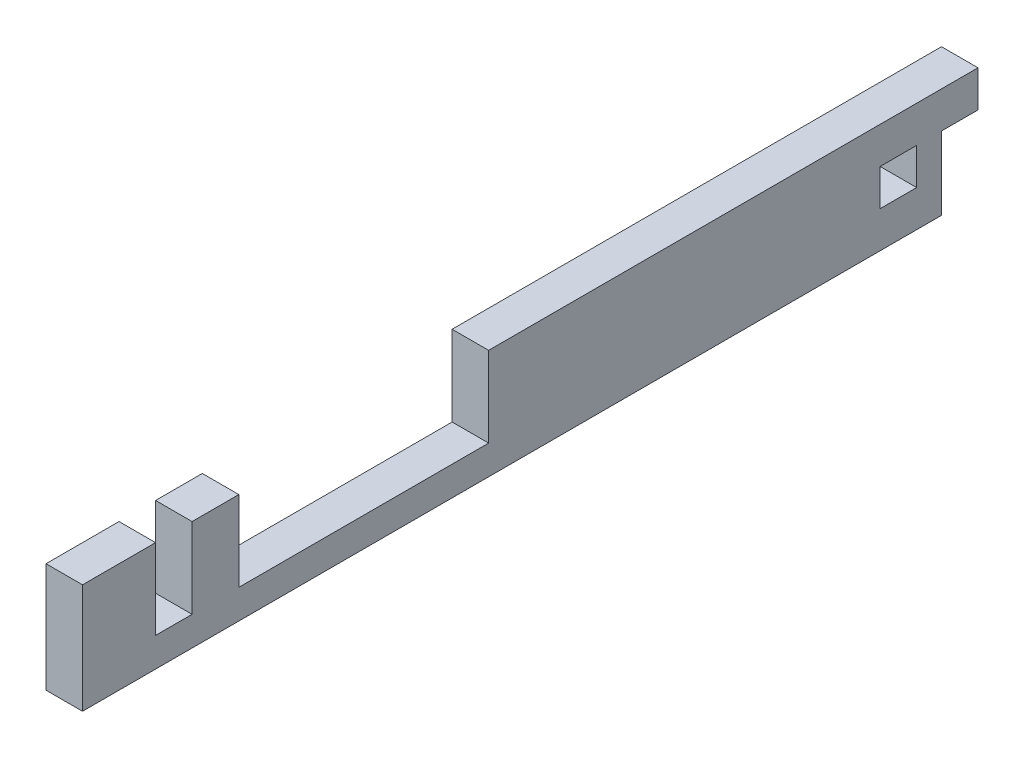
SolidWorks part; units mm, degrees
material "Acrylic (Medium-high impact)"
ref_plane "Front" through (0, 0, 0) normal (0, 0, 1) x (1, 0, 0)
ref_plane "Bottom" through (0, 0, 0) normal (0, 1, 0) x (1, 0, 0)
ref_plane "Right" through (0, 0, 0) normal (1, 0, 0) x (0, 0, -1)
sketch "Sketch1" plane through (0, 0, 0) normal (0, 1, 0) x (1, 0, 0)
  line L0 (-10.033, 66.167) -> (-11.6205, 66.167)
  line L2 (-11.6205, -66.167) -> (11.6205, -66.167)
  line L4 (11.6205, 66.167) -> (10.033, 66.167)
  line L5 (10.033, 66.167) -> (10.033, 59.817)
  line L6 (10.033, 59.817) -> (11.6205, 59.817)
  line L7 (11.6205, 59.817) -> (11.6205, -59.817)
  line L8 (11.6205, -59.817) -> (-11.6205, -59.817)
  line L9 (-11.6205, -59.817) -> (-11.6205, 59.817)
  line L10 (-11.6205, 59.817) -> (-10.033, 59.817)
  line L11 (-10.033, 59.817) -> (-10.033, 66.167)
  line L12 (-17.9705, -78.867) -> (-17.9705, 76.835)
  line L13 (-17.9705, 76.835) -> (-11.6205, 76.835)
  line L14 (-11.6205, 76.835) -> (-11.6205, 66.167)
  line L15 (11.6205, 66.167) -> (11.6205, 76.835)
  line L16 (11.6205, 76.835) -> (17.9705, 76.835)
  line L17 (17.9705, 76.835) -> (17.9705, -78.867)
  line L21 (-17.9705, -78.867) -> (-11.6205, -78.867)
  line L22 (-11.6205, -66.167) -> (-11.6205, -78.867)
  line L25 (17.9705, -78.867) -> (11.6205, -78.867)
  line L26 (11.6205, -66.167) -> (11.6205, -78.867)
  point P12 (0, -59.817)
  point P13 (-11.6205, 0)
  point P25 (-10.8267, 59.817)
  dimension "D1" = 6.35
  dimension "D2" = 6.35
  dimension "D3" = 6.35
  dimension "D4" = 1.5875
  dimension "D5" = 17.018
  dimension "D6" = 23.241
  dimension "D7" = 119.634
  dimension "D8" = 12.7
extrude "Boss-Extrude1" add sketch "Sketch1" along normal blind 19.05
sketch "Sketch2" plane through (-17.9705, 0, 0) normal (-1, 0, 0) x (0, 0, 1)
  line L0 (-76.835, 19.05) -> (78.867, 19.05) construction
  line L1 (8.255, 19.05) -> (51.689, 19.05)
  line L2 (8.255, 19.05) -> (8.255, 5.08)
  line L3 (8.255, 5.08) -> (51.689, 5.08)
  line L4 (51.689, 19.05) -> (51.689, 5.08)
  line L6 (-76.835, 0) -> (78.867, 0) construction
  dimension "D1" = 8.128
  dimension "D2" = 51.562
  dimension "D3" = 5.08
extrude "Motor Hole" cut sketch "Sketch2" against normal blind 19.05
sketch "Sketch3" plane through (-17.9705, 0, 0) normal (-1, 0, 0) x (0, 0, 1)
  line L0 (-76.835, 19.05) -> (-76.835, 0) construction
  line L1 (-76.835, 0) -> (-70.485, 0)
  line L2 (-76.835, 0) -> (-76.835, 12.7)
  line L3 (-76.835, 12.7) -> (-70.485, 12.7)
  line L4 (-70.485, 0) -> (-70.485, 12.7)
  line L6 (-76.835, 0) -> (78.867, 0) construction
  dimension "D1" = 12.7
  dimension "D2" = 6.35
extrude "Cut-Extrude2" cut sketch "Sketch3" against normal through all
sketch "Sketch5" plane through (-17.9705, 0, 0) normal (-1, 0, 0) x (0, 0, 1)
  line L0 (51.689, 19.05) -> (78.867, 19.05) construction
  line L1 (59.817, 19.05) -> (66.167, 19.05)
  line L2 (59.817, 19.05) -> (59.817, 5.08)
  line L3 (59.817, 5.08) -> (66.167, 5.08)
  line L4 (66.167, 19.05) -> (66.167, 5.08)
  line L5 (8.255, 5.08) -> (51.689, 5.08) construction
  line L6 (78.867, 19.05) -> (78.867, 0) construction
  line L7 (-66.167, 12.7) -> (-59.817, 12.7)
  line L8 (-66.167, 12.7) -> (-66.167, 6.35)
  line L9 (-66.167, 6.35) -> (-59.817, 6.35)
  line L10 (-59.817, 12.7) -> (-59.817, 6.35)
  point P18 (-66.167, 9.525)
  point P21 (78.867, 9.525)
  dimension "D1" = 6.35
extrude "Cut-Extrude6" cut sketch "Sketch5" against normal through all
sketch "Sketch7" plane through (0, 0, 0) normal (0, 1, 0) x (1, 0, 0)
  line L1 (-11.6205, -78.867) -> (38.637, -78.867)
  line L2 (-11.6205, -78.867) -> (-11.6205, 80.9204)
  line L3 (-11.6205, 80.9204) -> (38.637, 80.9204)
  line L4 (38.637, -78.867) -> (38.637, 80.9204)
extrude "Cut-Extrude7" cut sketch "Sketch7" along normal through all
